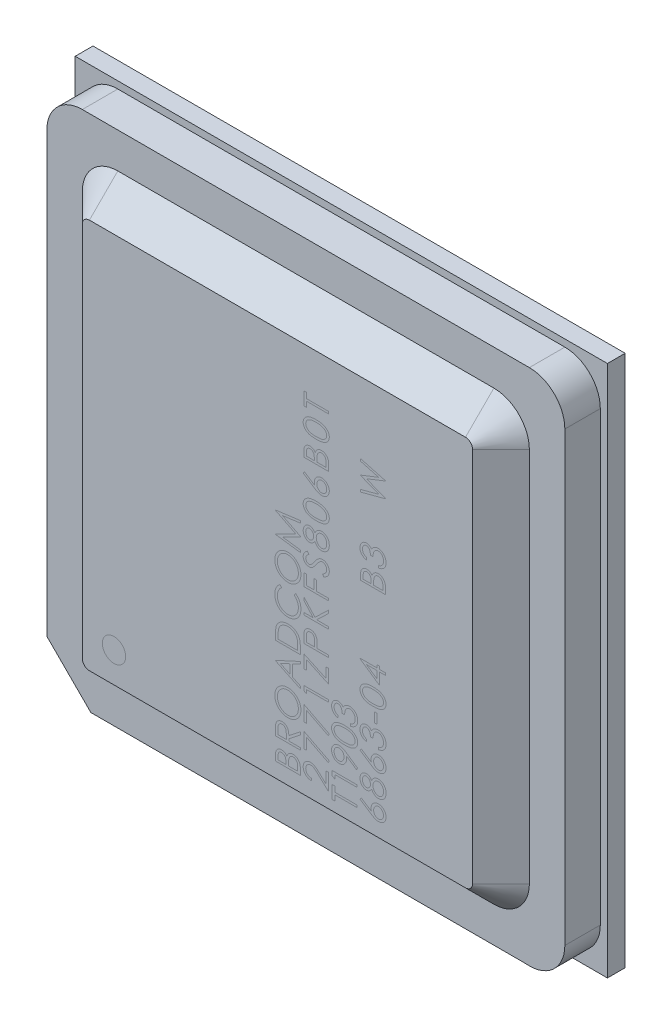
SolidWorks part; units mm, degrees
ref_plane "Płaszczyzna przednia" through (0, 0, 0) normal (0, 0, 1) x (1, 0, 0)
ref_plane "Płaszczyzna górna" through (0, 0, 0) normal (0, 1, 0) x (1, 0, 0)
ref_plane "Płaszczyzna prawa" through (0, 0, 0) normal (1, 0, 0) x (0, 0, -1)
sketch "Sketch2" plane through (0, 0, 0) normal (0, 0, 1) x (1, 0, 0)
  line L0 (-7.5, 7.5) -> (-7.5, -7.5)
  line L1 (-7.5, -7.5) -> (7.5, -7.5)
  line L2 (7.5, -7.5) -> (7.5, 7.5)
  line L3 (7.5, 7.5) -> (-7.5, 7.5)
  line L4 (0, 7.5) -> (0, -7.5) construction
  dimension "D1" = 15
  dimension "D2" = 15
  dimension "D3" = 15
  dimension "D4" = 15
extrude "Boss-Extrude1" add sketch "Sketch2" along normal blind 0.5
sketch "Sketch3" plane through (0, 0, 0.5) normal (0, 0, 1) x (1, 0, 0)
  line L6 (0, 0) -> (0, 7.5) construction
  line L7 (7.5, 7.5) -> (-7.5, 7.5) construction
  line L9 (7.3, -6.3062) -> (7.3, 6.3)
  line L10 (6.3, 7.3) -> (-6.3, 7.3)
  line L11 (-7.3, -6.06) -> (-7.3, 6.3)
  line L12 (7.05, -7.05) -> (-7.3, 7.3) construction
  line L13 (7.3, 7.3) -> (-7.3, -7.3) construction
  line L15 (-7.3, -6.06) -> (-6.06, -7.3)
  line L16 (-6.06, -7.3) -> (6.1884, -7.3)
  line L17 (-7.5, 0) -> (-2.6605, 0) construction
  line L18 (-7.5, 7.5) -> (-7.5, -7.5) construction
  arc A3 (7.3, -6.3062) -> (6.1884, -7.3) centre (6.3, -6.3062) cw
  arc A4 (6.3, 7.3) -> (7.3, 6.3) centre (6.3, 6.3) cw
  arc A5 (-7.3, 6.3) -> (-6.3, 7.3) centre (-6.3, 6.3) cw
  point P0 (0, 0)
  dimension "D1" = 1
  dimension "D2" = 1.24
  dimension "D3" = 1.24
  dimension "D4" = 14.6
  dimension "D5" = 14.6
extrude "Boss-Extrude2" add sketch "Sketch3" along normal blind 1
sketch "Sketch4" plane through (0, 0, 0.5) normal (0, 0, 1) x (1, 0, 0)
  line L0 (-7.5, -7.5) -> (-6.68, -6.68) construction
  line L1 (-7.3, -6.06) -> (-6.06, -7.3) construction
  circle A0 centre (-7.0135, -7.0135) radius 0.2
extrude "Cut-Extrude1" cut sketch "Sketch4" against normal blind 0.1
sketch "Sketch5" plane through (0, 0, 1.5) normal (0, 0, 1) x (1, 0, 0)
  line L1 (-5.3, -6.3) -> (5.3, -6.3)
  line L2 (-6.3, -5.3) -> (-6.3, 5.3)
  line L3 (-5.3, 6.3) -> (5.3, 6.3)
  line L4 (6.3, -5.3) -> (6.3, 5.3)
  line L5 (-6.3, -6.3) -> (6.3, 6.3) construction
  line L6 (-6.3, 6.3) -> (6.3, -6.3) construction
  arc A0 (-6.3, -5.3) -> (-5.3, -6.3) centre (-5.3, -5.3) ccw
  arc A1 (6.3, -5.3) -> (5.3, -6.3) centre (5.3, -5.3) cw
  arc A2 (6.3, 5.3) -> (5.3, 6.3) centre (5.3, 5.3) ccw
  arc A3 (-6.3, 5.3) -> (-5.3, 6.3) centre (-5.3, 5.3) cw
  point P0 (0, 0)
  dimension "D2" = 1
  dimension "D1" = 12.6
extrude "Boss-Extrude3" add sketch "Sketch5" along normal blind 0.8 draft 45
sketch "Szkic1" plane through (0, 0, 2.3) normal (0, 0, 1) x (1, 0, 0)
  line L0 (0.6432, -5.5) -> (0.6432, 5.5) construction
  line L1 (-5.3, -5.5) -> (5.3, -5.5) construction
  line L2 (5.3, 5.5) -> (-5.3, 5.5) construction
  line L3 (1.4432, -5.5) -> (1.4432, 5.5) construction
  line L4 (2.2432, -5.5) -> (2.2432, 5.5) construction
  line L5 (3.0432, -5.5) -> (3.0432, 5.5) construction
  circle A0 centre (-4.6073, -4.6463) radius 0.3289
  text T0 " BROADCOM\r\n" font "Century Gothic" height 0.7
  text T1 " 2771ZPKFS806B0T" font "Century Gothic" height 0.7
  text T2 " T1903" font "Century Gothic" height 0.7
  text T3 " 6863-04     B3   W" font "Century Gothic" height 0.7
  dimension "D2" = 0.8
  dimension "D1" = 0.8
  dimension "D3" = 0.8
split line "Linia podziałowa1"
